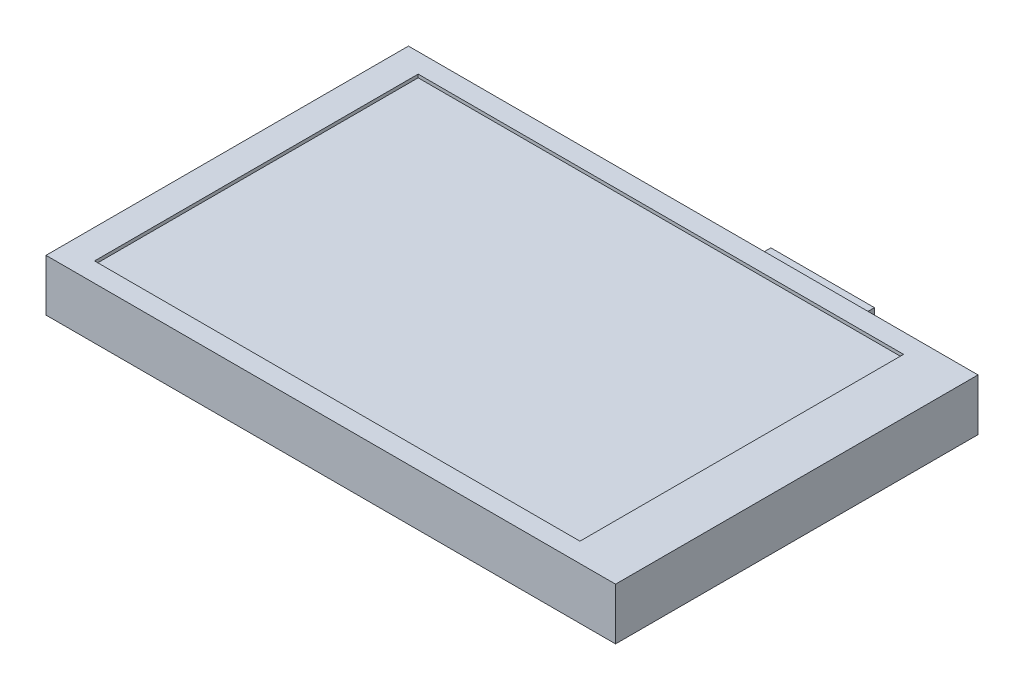
SolidWorks part; units mm, degrees
ref_plane "Front Plane" through (0, 0, 0) normal (0, 0, 1) x (1, 0, 0)
ref_plane "Top Plane" through (0, 0, 0) normal (0, 1, 0) x (1, 0, 0)
ref_plane "Right Plane" through (0, 0, 0) normal (1, 0, 0) x (0, 0, -1)
sketch "Sketch1" plane through (0, 0, 0) normal (0, 1, 0) x (1, 0, 0)
  line L1 (-44, 28) -> (44, 28)
  line L2 (-44, 28) -> (-44, -28)
  line L3 (-44, -28) -> (44, -28)
  line L4 (44, 28) -> (44, -28)
  line L5 (0, -28) -> (0, 28) construction
  line L6 (-44, 0) -> (44, 0) construction
  point P52 (0, 0)
  dimension "D1" = 88
  dimension "D2" = 56
extrude "Boss-Extrude1" add sketch "Sketch1" along normal blind 8
sketch "Sketch2" plane through (0, 8, 0) normal (0, 1, 0) x (1, 0, 0)
  line L1 (-39.5, 25) -> (35.5, 25)
  line L2 (-39.5, 25) -> (-39.5, -25)
  line L3 (-39.5, -25) -> (35.5, -25)
  line L4 (35.5, 25) -> (35.5, -25)
  line L5 (-2, -25) -> (-2, 25) construction
  line L6 (-39.5, 0) -> (35.5, 0) construction
  point P4 (-2, 6.358)
  point P5 (0, 0)
  dimension "D1" = 75
  dimension "D2" = 50
  dimension "D3" = 2
extrude "Cut-Extrude1" cut sketch "Sketch2" against normal blind 0.5
sketch "Sketch3" plane through (0, 0, 0) normal (0, 1, 0) x (1, 0, 0)
  line L0 (44, 28) -> (-44, 28) construction
  line L1 (3, 37) -> (19, 37)
  line L2 (3, 37) -> (3, 28)
  line L3 (3, 28) -> (19, 28)
  line L4 (19, 37) -> (19, 28)
  line L5 (11, 28) -> (11, 37) construction
  line L6 (3, 32.5) -> (19, 32.5) construction
  line L7 (44, -28) -> (44, 28) construction
  point P88 (11, 32.5)
  dimension "D1" = 9
  dimension "D2" = 16
  dimension "D3" = 33
extrude "Boss-Extrude2" add sketch "Sketch3" against normal blind 12 separate body
